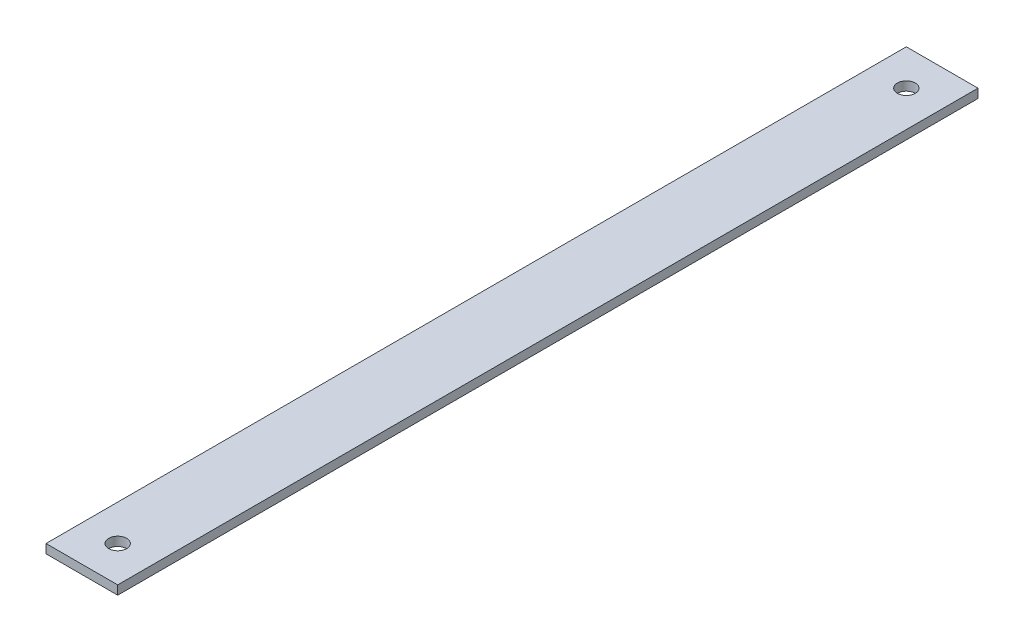
SolidWorks part; units mm, degrees
ref_plane "Front Plane" through (0, 0, 0) normal (0, 0, 1) x (1, 0, 0)
ref_plane "Top Plane" through (0, 0, 0) normal (0, 1, 0) x (1, 0, 0)
ref_plane "Right Plane" through (0, 0, 0) normal (1, 0, 0) x (0, 0, -1)
sketch "Sketch1" plane through (0, 0, 0) normal (0, 1, 0) x (1, 0, 0)
  line L1 (25.4, -304.8) -> (-25.4, -304.8)
  line L2 (25.4, -304.8) -> (25.4, 304.8)
  line L3 (25.4, 304.8) -> (-25.4, 304.8)
  line L4 (-25.4, -304.8) -> (-25.4, 304.8)
  line L5 (25.4, -304.8) -> (-25.4, 304.8) construction
  line L6 (25.4, 304.8) -> (-25.4, -304.8) construction
  point P0 (0, 0)
  dimension "D1" = 609.6
  dimension "D2" = 50.8
extrude "Boss-Extrude1" add sketch "Sketch1" along normal blind 6.35
sketch "Sketch2" plane through (0, 6.35, 0) normal (0, 1, 0) x (1, 0, 0)
  line L0 (0, -279.4) -> (0, 279.4) construction
  circle A0 centre (0, 279.4) radius 6.35
  circle A1 centre (0, -279.4) radius 6.35
  point P4 (0, 0)
  dimension "D1" = 12.7
  dimension "D2" = 558.8
extrude "Cut-Extrude1" cut sketch "Sketch2" against normal through all
